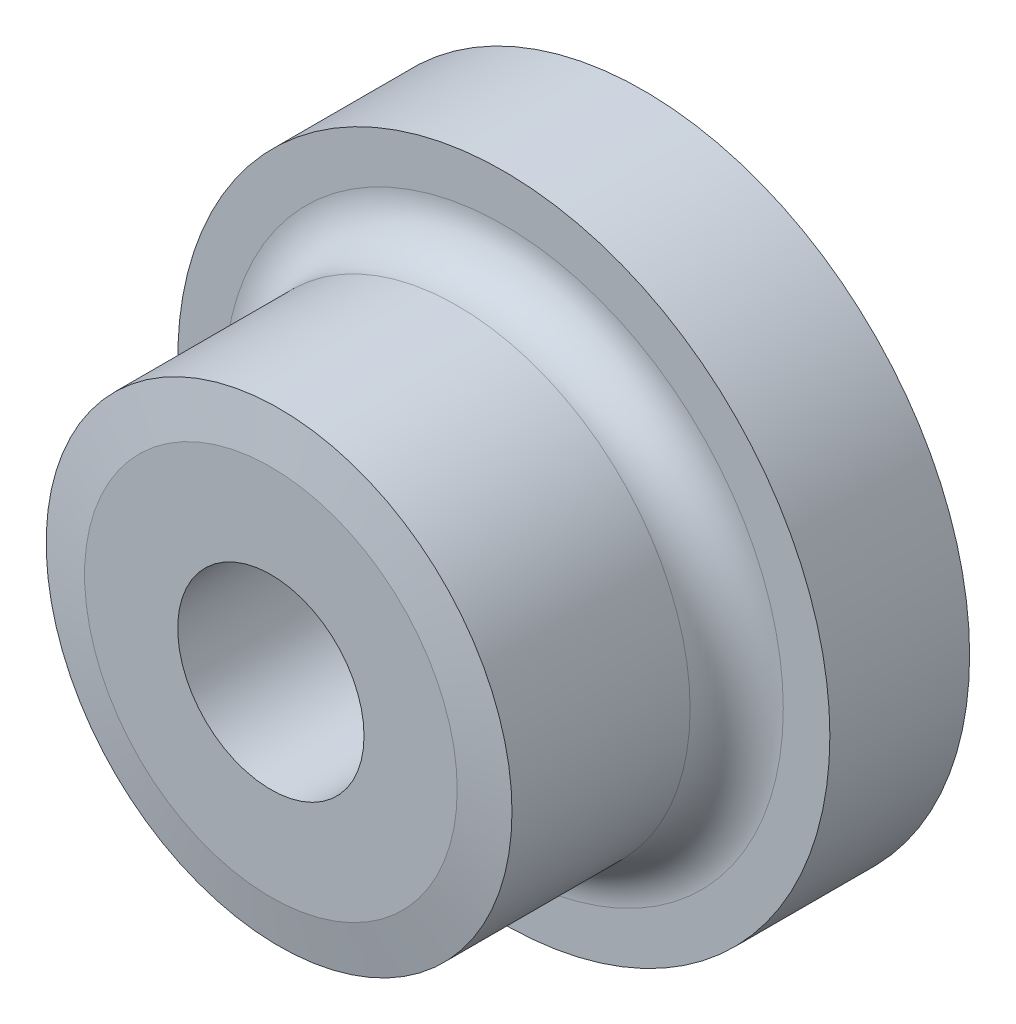
SolidWorks part; units mm, degrees
ref_plane "Plan de face" through (0, 0, 0) normal (0, 0, 1) x (1, 0, 0)
ref_plane "Plan de dessus" through (0, 0, 0) normal (0, 1, 0) x (1, 0, 0)
ref_plane "Plan de droite" through (0, 0, 0) normal (1, 0, 0) x (0, 0, -1)
sketch "Esquisse1" plane through (0, 0, 0) normal (0, 0, 1) x (1, 0, 0)
  circle A0 centre (0, 0) radius 7
  dimension "D1" = 14
extrude "Boss.-Extru.1" add sketch "Esquisse1" along normal blind 3
sketch "Esquisse2" plane through (0, 0, 3) normal (0, 0, 1) x (1, 0, 0)
  circle A0 centre (0, 0) radius 5
  dimension "D1" = 10
extrude "Boss.-Extru.2" add sketch "Esquisse2" along normal blind 5
sketch "Esquisse3" plane through (0, 0, 8) normal (0, 0, 1) x (1, 0, 0)
  circle A0 centre (0, 0) radius 2
  dimension "D1" = 4
extrude "Enlèv. mat.-Extru.1" cut sketch "Esquisse3" against normal through all
fillet "Congé1" radius 1 1 edges at (5, 0, 3)
chamfer "Chanfrein1" distance 1 angle 10 1 edges at (5, 0, 8)
